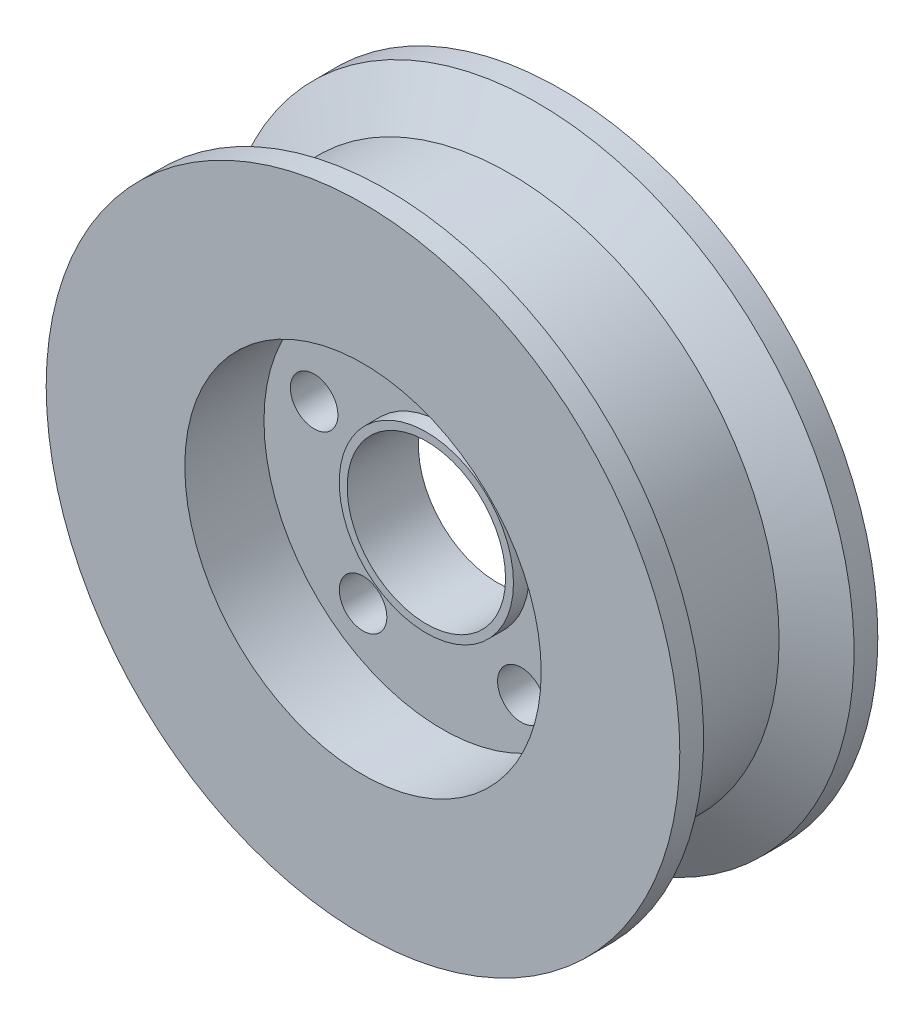
SolidWorks part; units mm, degrees
ref_plane "Front Plane" through (0, 0, 0) normal (0, 0, 1) x (1, 0, 0)
ref_plane "Top Plane" through (0, 0, 0) normal (0, 1, 0) x (1, 0, 0)
ref_plane "Right Plane" through (0, 0, 0) normal (1, 0, 0) x (0, 0, -1)
sketch "Sketch1" plane through (0, 0, 0) normal (0, 0, 1) x (1, 0, 0)
  circle A0 centre (0, 0) radius 10
  circle A1 centre (0, 0) radius 40
  dimension "D1" = 80
  dimension "D2" = 20
extrude "Boss-Extrude1" add sketch "Sketch1" along normal mid plane 25
sketch "Sketch2" plane through (0, 0, 12.5) normal (0, 0, 1) x (1, 0, 0)
  circle A0 centre (0, 0) radius 22.5
  circle A1 centre (0, 0) radius 40 construction
  dimension "D1" = 17.5
extrude "Cut-Extrude1" cut sketch "Sketch2" against normal blind 10
mirror "Mirror1" about plane through (0, 0, 0) normal (0, 0, 1) of "Cut-Extrude1"
sketch "Sketch4" plane through (0, 0, 2.5) normal (0, 0, 1) x (1, 0, 0)
  circle A0 centre (0, 17) radius 3
  dimension "D2" = 6
  dimension "D1" = 17
extrude "Cut-Extrude2" cut sketch "Sketch4" against normal through all
pattern_circular "CirPattern1" count 5 over 360 about axis through (0, 0, 0) along (0, 0, 1) of "Cut-Extrude2"
sketch "Sketch5" plane through (0, 0, 2.5) normal (0, 0, 1) x (1, 0, 0)
  circle A0 centre (0, 0) radius 11
  circle A1 centre (0, 0) radius 10 construction
  circle A2 centre (0, 0) radius 10
  dimension "D1" = 22
extrude "Boss-Extrude2" add sketch "Sketch5" along normal blind 2 and the other way blind 7
sketch "Sketch6" plane through (0, 0, 0) normal (0, 1, 0) x (1, 0, 0)
  line L0 (0, 24.4058) -> (0, -21.602) construction
  line L1 (-40, 9.5) -> (-34, 6.0359)
  line L2 (-40, 12.5) -> (-40, -12.5) construction
  line L3 (-34, 6.0359) -> (-34, -6.0359)
  line L4 (-34, -6.0359) -> (-40, -9.5)
  line L5 (-40, -9.5) -> (-40, 9.5)
  dimension "D1" = 3
  dimension "D2" = 3
  dimension "D3" = 6
  dimension "D4" = 60
  dimension "D5" = 60
revolve "Cut-Revolve1" cut sketch "Sketch6" angle 360 about L0
